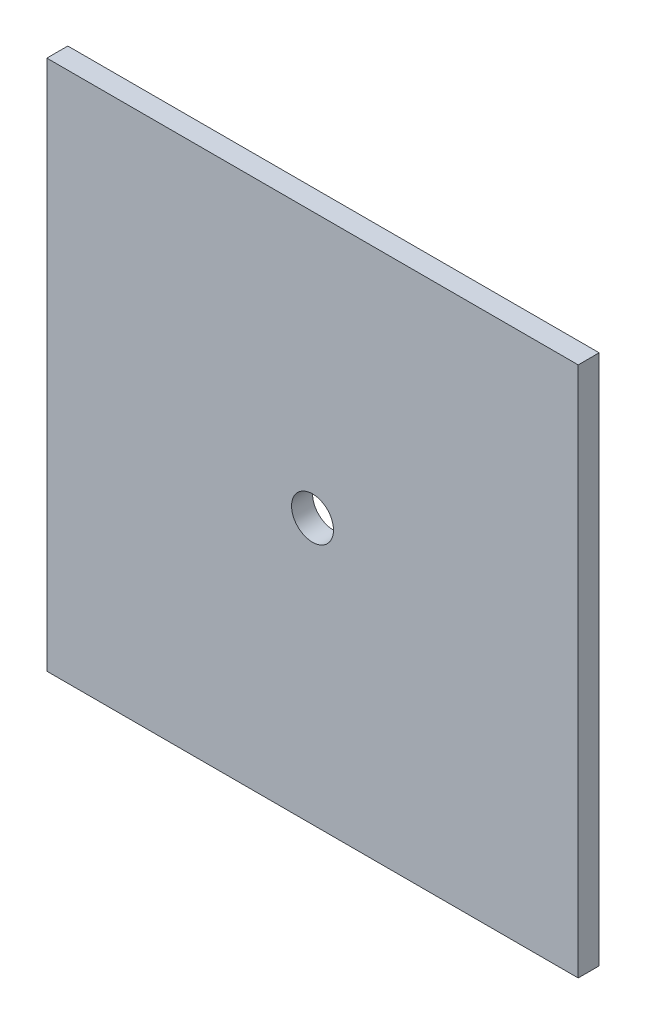
SolidWorks part; units mm, degrees
ref_plane "Front Plane" through (0, 0, 0) normal (0, 0, 1) x (1, 0, 0)
ref_plane "Top Plane" through (0, 0, 0) normal (0, 1, 0) x (1, 0, 0)
ref_plane "Right Plane" through (0, 0, 0) normal (1, 0, 0) x (0, 0, -1)
sketch "Sketch1" plane through (0, 0, 0) normal (0, 0, 1) x (1, 0, 0)
  line L1 (38.027, -38) -> (-38.027, -38)
  line L2 (38.027, -38) -> (38.027, 38)
  line L3 (38.027, 38) -> (-38.027, 38)
  line L4 (-38.027, -38) -> (-38.027, 38)
  line L5 (38.027, -38) -> (-38.027, 38) construction
  line L6 (38.027, 38) -> (-38.027, -38) construction
  point P0 (0, 0)
extrude "Boss-Extrude2" add sketch "Sketch1" along normal blind 3
sketch "Sketch3" plane through (0, 0, 3) normal (0, 0, 1) x (1, 0, 0)
  circle A0 centre (0, 0) radius 3
extrude "Cut-Extrude1" cut sketch "Sketch3" against normal through all
